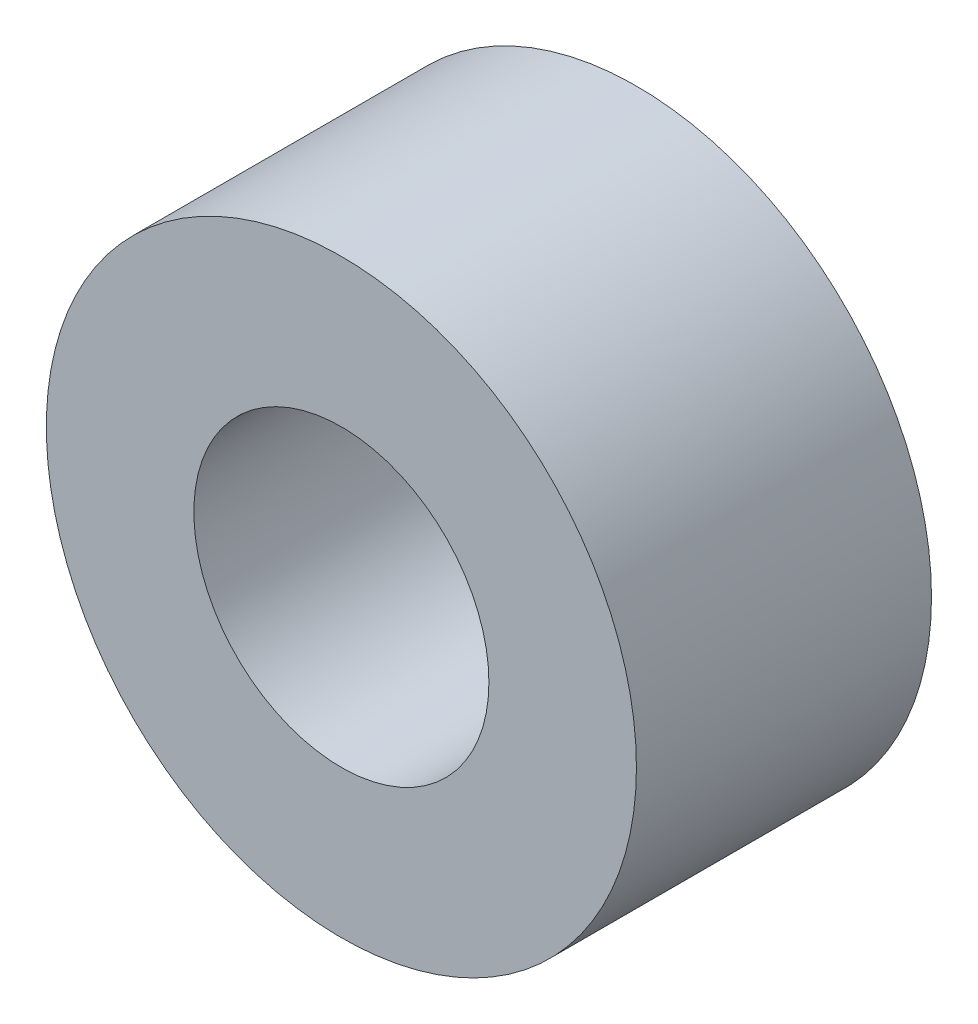
SolidWorks part; units mm, degrees
material "Nylon 6/10"
ref_plane "Front Plane" through (0, 0, 0) normal (0, 0, 1) x (1, 0, 0)
ref_plane "Top Plane" through (0, 0, 0) normal (0, 1, 0) x (1, 0, 0)
ref_plane "Right Plane" through (0, 0, 0) normal (1, 0, 0) x (0, 0, -1)
sketch "Sketch1" plane through (0, 0, 0) normal (0, 0, 1) x (1, 0, 0)
  circle A0 centre (0, 0) radius 1.5
  circle A1 centre (0, 0) radius 3
  dimension "D1" = 6
  dimension "D2" = 3
extrude "Boss-Extrude1" add sketch "Sketch1" along normal mid plane 3
